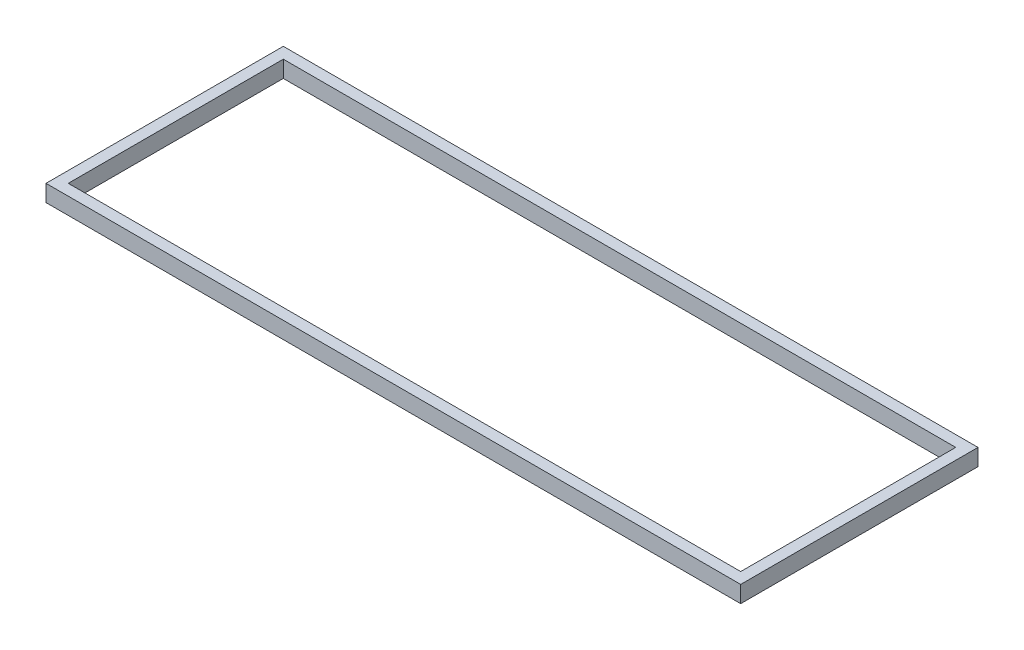
SolidWorks part; units mm, degrees
ref_plane "Plan de face" through (0, 0, 0) normal (0, 0, 1) x (1, 0, 0)
ref_plane "Plan de dessus" through (0, 0, 0) normal (0, 1, 0) x (1, 0, 0)
ref_plane "Plan de droite" through (0, 0, 0) normal (1, 0, 0) x (0, 0, -1)
sketch "Esquisse1" plane through (0, 0, 0) normal (0, 1, 0) x (1, 0, 0)
  line L1 (0, 0) -> (249.56, 0)
  line L2 (0, 0) -> (0, 85.25)
  line L3 (0, 85.25) -> (249.56, 85.25)
  line L4 (249.56, 0) -> (249.56, 85.25)
  line L5 (4, 81.25) -> (245.56, 81.25)
  line L6 (4, 81.25) -> (4, 4)
  line L7 (4, 4) -> (245.56, 4)
  line L8 (245.56, 81.25) -> (245.56, 4)
  dimension "D1" = 249.56
  dimension "D2" = 85.25
  dimension "D3" = 4
  dimension "D4" = 4
  dimension "D5" = 4
  dimension "D6" = 4
extrude "Boss.-Extru.1" add sketch "Esquisse1" along normal blind 6
